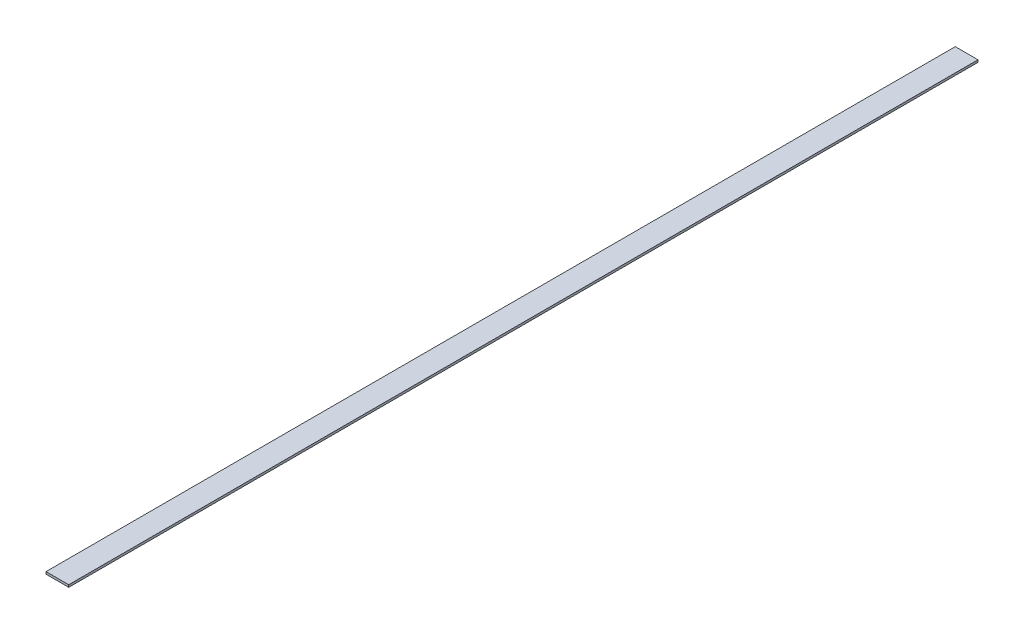
SolidWorks part; units mm, degrees
material "Balsa"
ref_plane "Front Plane" through (0, 0, 0) normal (0, 0, 1) x (1, 0, 0)
ref_plane "Top Plane" through (0, 0, 0) normal (0, 1, 0) x (1, 0, 0)
ref_plane "Right Plane" through (0, 0, 0) normal (1, 0, 0) x (0, 0, -1)
sketch "Sketch1" plane through (0, 0, 0) normal (0, 0, 1) x (1, 0, 0)
  line L1 (-15, 1.5) -> (15, 1.5)
  line L2 (-15, 1.5) -> (-15, -1.5)
  line L3 (-15, -1.5) -> (15, -1.5)
  line L4 (15, 1.5) -> (15, -1.5)
  line L5 (-15, 1.5) -> (15, -1.5) construction
  line L6 (-15, -1.5) -> (15, 1.5) construction
  point P0 (0, 0)
  dimension "D1" = 30
  dimension "D2" = 3
extrude "Boss-Extrude1" add sketch "Sketch1" along normal blind 1200
